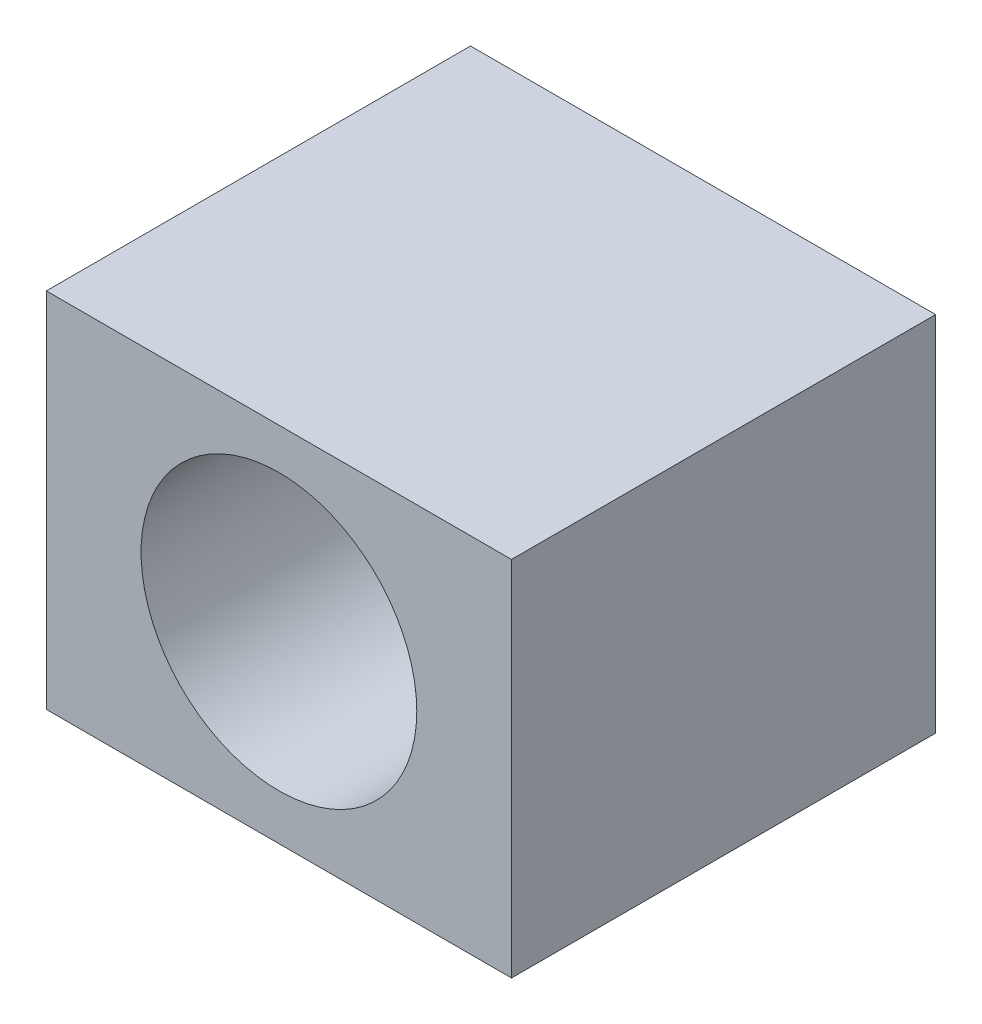
SolidWorks part; units mm, degrees
ref_plane "前视基准面" through (0, 0, 0) normal (0, 0, 1) x (1, 0, 0)
ref_plane "上视基准面" through (0, 0, 0) normal (0, 1, 0) x (1, 0, 0)
ref_plane "右视基准面" through (0, 0, 0) normal (1, 0, 0) x (0, 0, -1)
other "Configuration Table"
sketch "草图1" plane through (0, 0, 0) normal (0, 0, 1) x (1, 0, 0)
  line L1 (-45.507, 33.7281) -> (42.2328, 33.7281)
  line L2 (-45.507, 33.7281) -> (-45.507, -34.6405)
  line L3 (-45.507, -34.6405) -> (42.2328, -34.6405)
  line L4 (42.2328, 33.7281) -> (42.2328, -34.6405)
  circle A0 centre (-1.6371, 0) radius 26
extrude "凸台-拉伸1" add sketch "草图1" along normal blind 80
